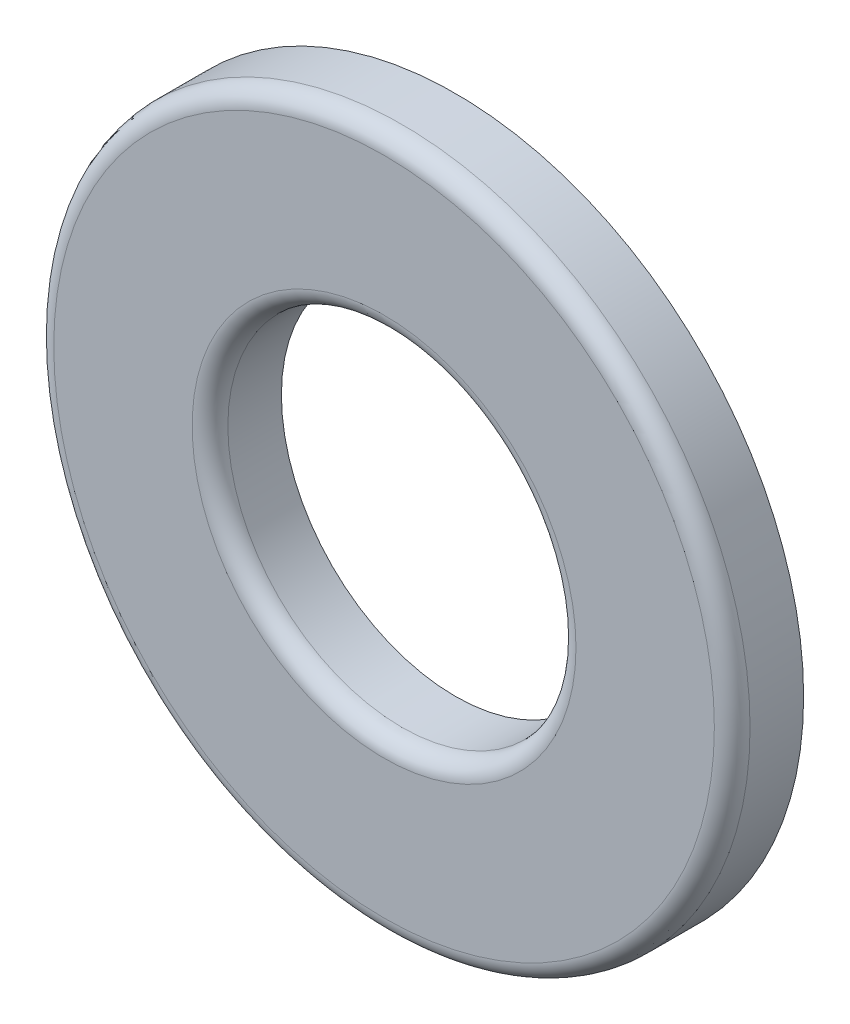
SolidWorks part; units mm, degrees
other "Imported1" parameters "D1"=0.2032, "TH"=1.0287, "Thickness"=0.8128
material "Alloy Steel (SS)"
ref_plane "Front Plane" through (0, 0, 0) normal (0, 0, 1) x (1, 0, 0)
ref_plane "Top Plane" through (0, 0, 0) normal (0, 1, 0) x (1, 0, 0)
ref_plane "Right Plane" through (0, 0, 0) normal (1, 0, 0) x (0, 0, -1)
sketch "Sketch1" plane through (0, 0, 0) normal (0, 0, 1) x (1, 0, 0)
  line L0 (-3.9624, 0) -> (3.9624, 0) construction
  line L1 (-1.9812, 0) -> (1.9812, 0) construction
  circle A0 centre (0, 0) radius 1.9812 construction
  circle A1 centre (0, 0) radius 3.9624 construction
  point P8 (0, 0)
  point P9 (0, 3.9624)
  point P11 (1.9812, 0)
  dimension "ID" = 3.9624
  dimension "OD" = 7.9248
sketch "Sketch2" plane through (0, 0, 0) normal (1, 0, 0) x (0, 0, -1)
  line L0 (-0.4064, 3.9624) -> (0.4064, 3.9624) construction
  point P2 (0, 3.9624)
sketch "Sketch3" plane through (0, 0, 0) normal (0, 0, 1) x (1, 0, 0)
  circle A0 centre (0, 0) radius 1.9812
  circle A1 centre (0, 0) radius 3.9624
extrude "Boss-Extrude1" add sketch "Sketch3" along normal up to vertex (0.4064 mm away) and the other way up to vertex (0.4064 mm away) up to point (0, 3.9624, 0.4064) other way up to point (0, 3.9624, -0.4064)
fillet "Fillet1" radius 0.2032 2 edges at (3.9624, 0, 0.4064) (1.9812, 0, 0.4064)
equation "\"D1@Fillet1\"=\"Thickness@Sketch2\"/4"
